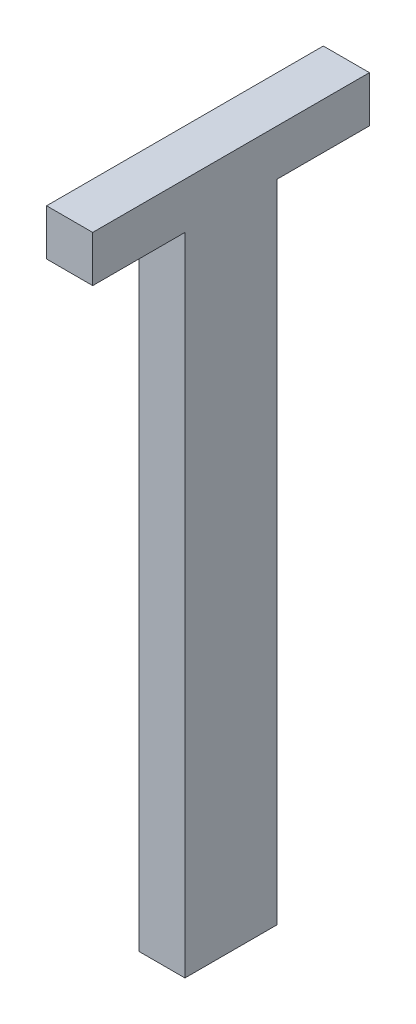
SolidWorks part; units mm, degrees
ref_plane "前视基准面" through (0, 0, 0) normal (0, 0, 1) x (1, 0, 0)
ref_plane "上视基准面" through (0, 0, 0) normal (0, 1, 0) x (1, 0, 0)
ref_plane "右视基准面" through (0, 0, 0) normal (1, 0, 0) x (0, 0, -1)
sketch "草图1" plane through (0, 0, 0) normal (0, 1, 0) x (1, 0, 0)
  line L1 (0, 0) -> (5, 0)
  line L2 (0, 0) -> (0, 10)
  line L3 (0, 10) -> (5, 10)
  line L4 (5, 0) -> (5, 10)
extrude "凸台-拉伸1" add sketch "草图1" along normal blind 70
sketch "草图2" plane through (0, 70, 0) normal (0, 1, 0) x (1, 0, 0)
  line L1 (0, 10) -> (5, 10)
  line L2 (0, 10) -> (0, 0)
  line L3 (0, 0) -> (5, 0)
  line L4 (5, 10) -> (5, 0)
  line L5 (0, 0) -> (5, 0)
  line L6 (0, 0) -> (0, -10)
  line L7 (0, -10) -> (5, -10)
  line L8 (5, 0) -> (5, -10)
  line L9 (0, 10) -> (5, 10)
  line L10 (0, 10) -> (0, 20)
  line L11 (0, 20) -> (5, 20)
  line L12 (5, 10) -> (5, 20)
  line M9 (0, 10) -> (0, 0)
  line M10 (0, 0) -> (5, 0)
  line M11 (5, 0) -> (5, 10)
  line M12 (5, 10) -> (0, 10)
extrude "凸台-拉伸2" add sketch "草图2" along normal blind 5 contours L12 L11 L10 M12 | M12 M9 M10 M11 | L8 L6 L7 M10
